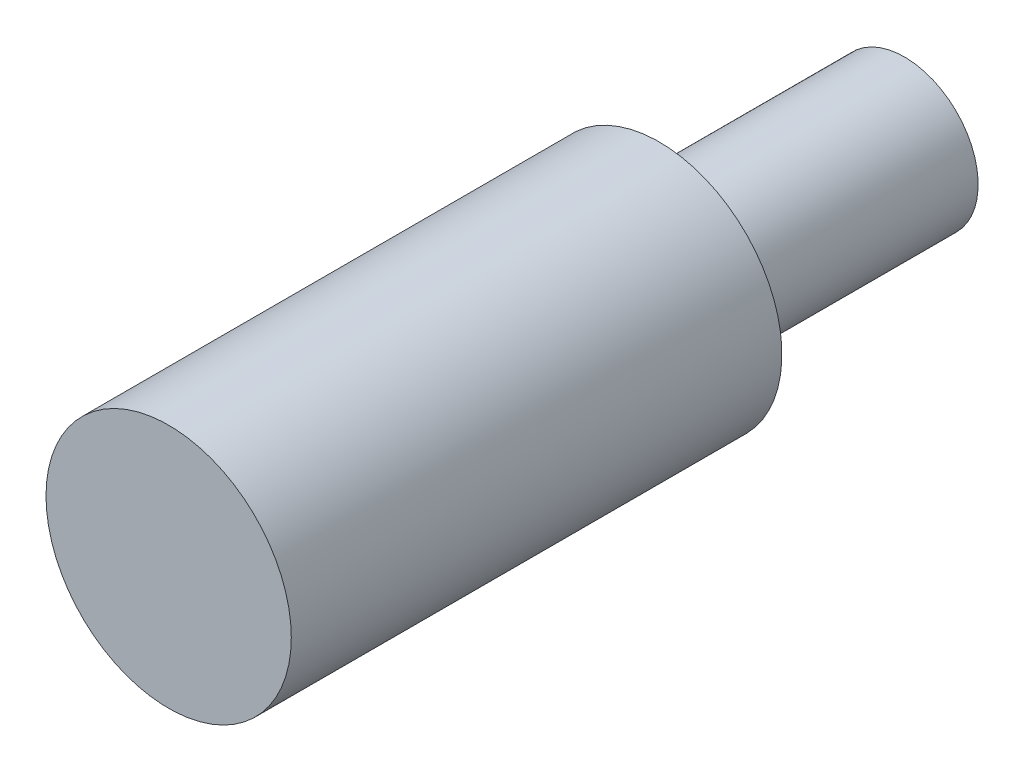
SolidWorks part; units mm, degrees
ref_plane "正面" through (0, 0, 0) normal (0, 0, 1) x (1, 0, 0)
ref_plane "平面" through (0, 0, 0) normal (0, 1, 0) x (1, 0, 0)
ref_plane "右側面" through (0, 0, 0) normal (1, 0, 0) x (0, 0, -1)
sketch "ｽｹｯﾁ1" plane through (0, 0, 0) normal (0, 0, 1) x (1, 0, 0)
  circle A0 centre (0, 14.208) radius 25
extrude "ﾎﾞｽ - 押し出し1" add sketch "ｽｹｯﾁ1" along normal blind 150
sketch "ｽｹｯﾁ2" plane through (0, 0, 0) normal (0, 0, -1) x (-1, 0, 0)
  circle A0 centre (0, 14.208) radius 15
  circle A1 centre (0, 14.208) radius 25 construction
  circle A2 centre (0, 14.208) radius 25
  dimension "D1" = 0
  dimension "D2" = 0
  dimension "D3" = 10
  dimension "D5" = 0
  dimension "D6" = 0
  dimension "D4" = 0
extrude "ｶｯﾄ - 押し出し1" cut sketch "ｽｹｯﾁ2" against normal blind 50
